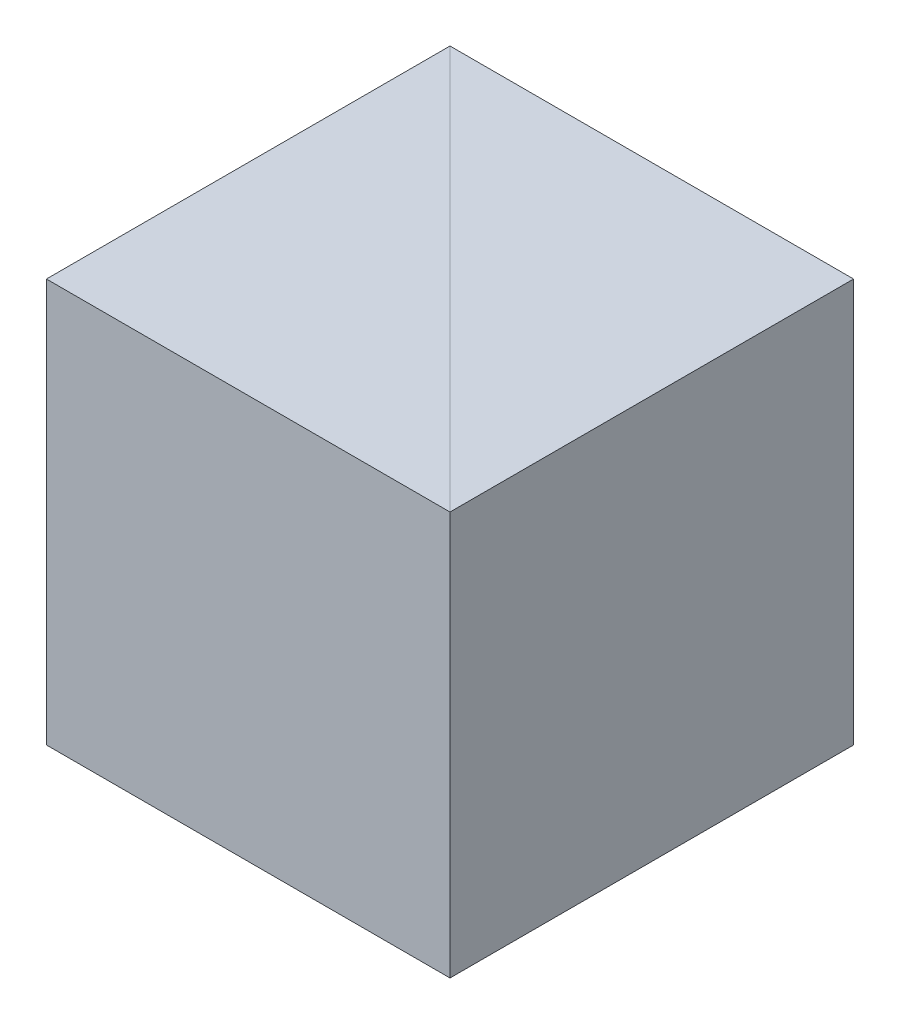
SolidWorks part; units mm, degrees
ref_plane "前视基准面" through (0, 0, 0) normal (0, 0, 1) x (1, 0, 0)
ref_plane "上视基准面" through (0, 0, 0) normal (0, 1, 0) x (1, 0, 0)
ref_plane "右视基准面" through (0, 0, 0) normal (1, 0, 0) x (0, 0, -1)
sketch "草图1" plane through (0, 0, 0) normal (0, 1, 0) x (1, 0, 0)
  line L0 (0, 0) -> (0, 50)
  line L1 (0, 50) -> (-50, 50)
  line L2 (-50, 50) -> (0, 0)
  dimension "D1" = 50
  dimension "D2" = 50
extrude "凸台-拉伸1" add sketch "草图1" along normal blind 50
sketch "草图2" plane through (0, 0, 0) normal (0, -1, 0) x (1, 0, 0)
  line L0 (-50, -50) -> (-50, 0)
  line L1 (-50, 0) -> (0, 0)
  line L2 (0, 0) -> (-50, -50)
extrude "凸台-拉伸2" add sketch "草图2" against normal blind 50 separate body
